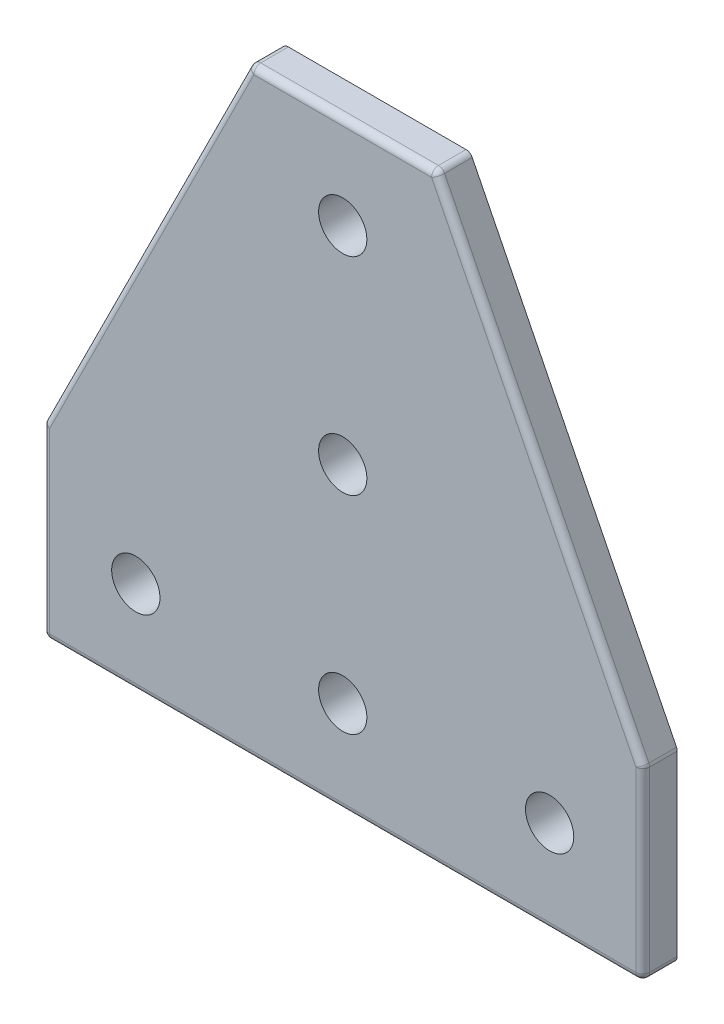
SolidWorks part; units mm, degrees
material "6061-T6 (SS)"
ref_plane "Front Plane" through (0, 0, 0) normal (0, 0, 1) x (1, 0, 0)
ref_plane "Top Plane" through (0, 0, 0) normal (0, 1, 0) x (1, 0, 0)
ref_plane "Right Plane" through (0, 0, 0) normal (1, 0, 0) x (0, 0, -1)
sketch "Sketch1" plane through (0, 0, 0) normal (0, 0, 1) x (1, 0, 0)
  line L0 (0, 0) -> (0, 27)
  line L1 (13.5, 13.5) -> (43.5, 13.5) construction
  line L2 (43.5, 13.5) -> (73.5, 13.5) construction
  line L3 (43.5, 13.5) -> (43.5, 43.5) construction
  line L4 (57, 87) -> (30, 87)
  line L5 (87, 0) -> (0, 0)
  line L6 (43.5, 43.5) -> (43.5, 73.5) construction
  line L7 (87, 27) -> (87, 0)
  line L8 (57, 87) -> (87, 27)
  line L9 (87, 13.5) -> (73.5, 13.5) construction
  line L10 (43.5, 87) -> (43.5, 73.5) construction
  line L11 (0, 27) -> (30, 87)
  circle A0 centre (13.5, 13.5) radius 3.5
  circle A1 centre (43.5, 13.5) radius 3.5
  circle A2 centre (73.5, 13.5) radius 3.5
  circle A3 centre (43.5, 43.5) radius 3.5
  circle A4 centre (43.5, 73.5) radius 3.5
  dimension "D1" = 30
  dimension "E" = 7
  dimension "D2" = 13.5
  dimension "C" = 87
  dimension "D3" = 30
  dimension "B" = 87
  dimension "D4" = 13.5
  dimension "D5" = 27
extrude "Boss-Extrude1" add sketch "Sketch1" along normal mid plane 5
fillet "Fillet1" radius 1 12 edges at (0, 0, 0) (0, 13.5, 2.5) (43.5, 0, 2.5) (87, 13.5, 2.5) (87, 0, 0) (43.5, 87, 2.5) (72, 57, 2.5) (87, 27, 0) (57, 87, 0) (15, 57, 2.5) (30, 87, 0) (0, 27, 0)
